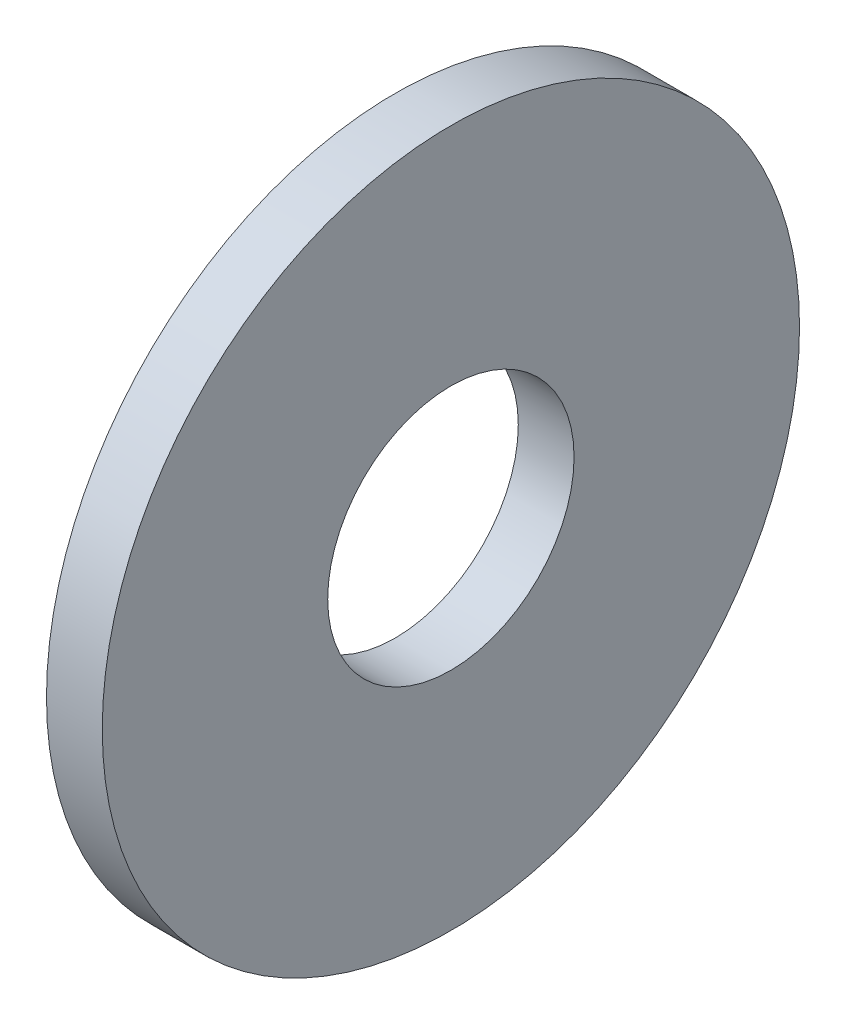
SolidWorks part; units mm, degrees
ref_plane "Plane1" through (0, 0, 0) normal (0, 0, 1) x (1, 0, 0)
ref_plane "Plane2" through (0, 0, 0) normal (0, 1, 0) x (1, 0, 0)
ref_plane "Plane3" through (0, 0, 0) normal (1, 0, 0) x (0, 0, -1)
sketch "Sketch1" plane through (0, 0, 0) normal (0, 0, 1) x (1, 0, 0)
  line L0 (-34.925, 0) -> (9.525, 0) construction
  line L1 (0, 2.65) -> (0, 7.5)
  line L2 (0, 7.5) -> (-1.2, 7.5)
  line L3 (-1.2, 7.5) -> (-1.2, 2.65)
  line L4 (-1.2, 2.65) -> (0, 2.65)
  dimension "Thickness" = 1.2
  dimension "Inside_dia" = 5.3
  dimension "Outside_dia" = 15
revolve "Base-Revolve" add sketch "Sketch1" angle 360 about L0
